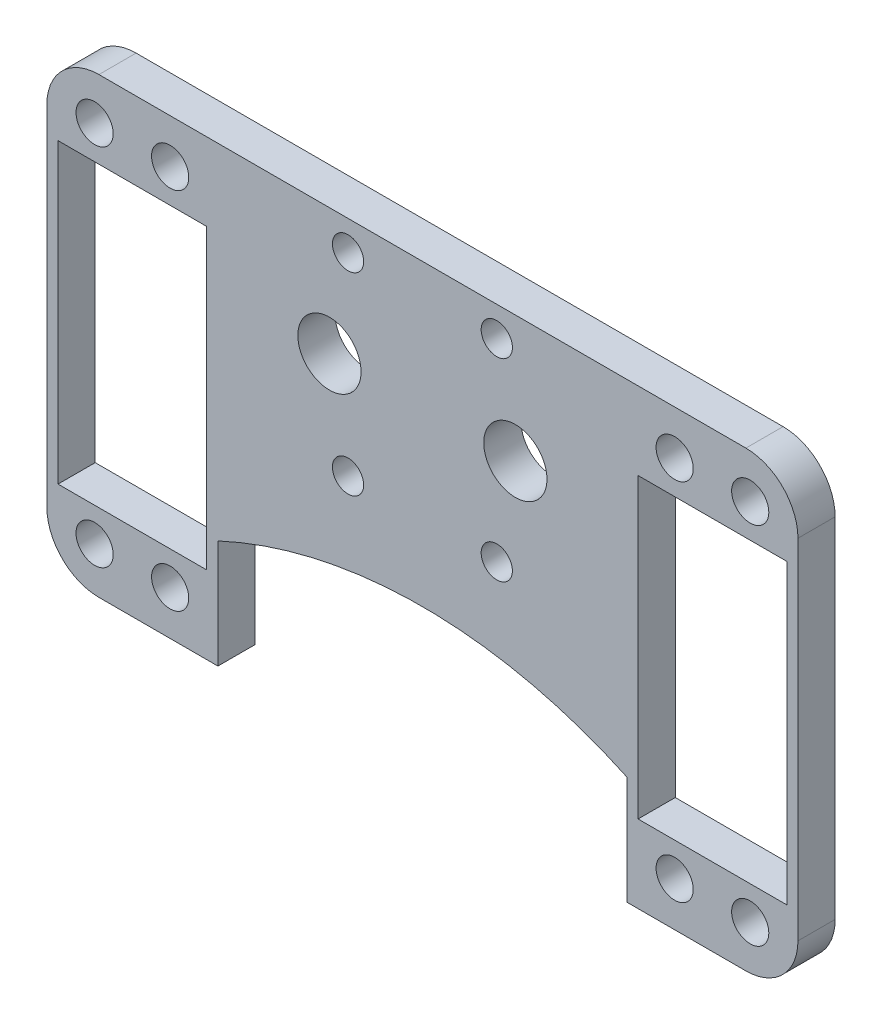
SolidWorks part; units mm, degrees
ref_plane "Front Plane" through (0, 0, 0) normal (0, 0, 1) x (1, 0, 0)
ref_plane "Top Plane" through (0, 0, 0) normal (0, 1, 0) x (1, 0, 0)
ref_plane "Right Plane" through (0, 0, 0) normal (1, 0, 0) x (0, 0, -1)
sketch "Sketch1" plane through (0, 0, 0) normal (0, 0, 1) x (1, 0, 0)
  line L14 (27.058, 13.3488) -> (18.058, 13.3488)
  line L15 (18.058, 13.3488) -> (18.058, 18.3488)
  line L16 (18.058, 18.3488) -> (-18.942, 18.3488)
  line L17 (-18.942, 18.3488) -> (-18.942, 13.3488)
  line L18 (-18.942, 13.3488) -> (-27.942, 13.3488)
  line L19 (-27.942, 13.3488) -> (-27.942, 1.3488)
  line L20 (27.058, 1.3488) -> (27.058, 13.3488)
  line L26 (27.058, -10.6512) -> (27.058, 1.3488)
  line L27 (-27.942, 1.3488) -> (-27.942, -10.6512)
  line L28 (-0.442, -25.6512) -> (-0.442, -85.6512) construction
  line L29 (-27.942, -10.6512) -> (-63.2973, -46.0066)
  line L34 (-63.2973, -46.0066) -> (-51.2973, -58.0066)
  line L35 (62.4134, -46.0066) -> (50.4134, -58.0066)
  line L37 (27.058, -10.6512) -> (62.4134, -46.0066)
  line L38 (-51.2973, -58.0066) -> (50.4134, -58.0066)
  arc A5 (-8.692, 1.3488) -> (-17.192, 1.3488) centre (-12.942, 1.3488) ccw
  arc A6 (16.308, 1.3488) -> (7.808, 1.3488) centre (12.058, 1.3488) ccw
  arc A7 (7.808, 1.3488) -> (16.308, 1.3488) centre (12.058, 1.3488) ccw
  arc A8 (-17.192, 1.3488) -> (-8.692, 1.3488) centre (-12.942, 1.3488) ccw
  circle A9 centre (9.558, -11.6512) radius 2.1
  circle A10 centre (-10.442, -11.6512) radius 2.1
  circle A11 centre (-10.442, 14.3488) radius 2.1
  circle A12 centre (9.558, 14.3488) radius 2.1
  dimension "D1" = 60
  dimension "D4" = 50
extrude "Boss-Extrude1" add sketch "Sketch1" along normal blind 5
sketch "Sketch2" plane through (0, 0, 0) normal (0, 0, -1) x (-1, 0, 0)
  line L0 (-27.058, -22.4869) -> (-27.058, -151.2309)
  line L2 (0.442, -156.8589) -> (0.442, -140.8235) construction
  line L3 (27.942, -22.4869) -> (27.942, -151.2309)
  arc A0 (-27.058, -151.2309) -> (27.942, -151.2309) centre (0.442, -86.8589) ccw
  arc A1 (27.942, -22.4869) -> (-27.058, -22.4869) centre (0.442, -86.8589) ccw
  dimension "D1" = 140
extrude "Cut-Extrude1" cut sketch "Sketch2" against normal blind 5
sketch "Sketch3" plane through (0, 0, 0) normal (0, 0, -1) x (-1, 0, 0)
  line L0 (0.442, -21.8589) -> (0.442, -31.1554) construction
  line L1 (-27.058, -27.5381) -> (-65.3095, -27.5381)
  line L2 (-27.058, -27.5381) -> (-27.058, -60.3042)
  line L3 (-27.058, -60.3042) -> (-65.3095, -60.3042)
  line L4 (-65.3095, -27.5381) -> (-65.3095, -60.3042)
  line L5 (-27.058, -27.5381) -> (-65.3095, -60.3042) construction
  line L6 (-27.058, -60.3042) -> (-65.3095, -27.5381) construction
  line L7 (27.942, -60.3042) -> (66.1934, -27.5381) construction
  line L8 (27.942, -27.5381) -> (66.1934, -60.3042) construction
  line L9 (66.1934, -27.5381) -> (66.1934, -60.3042)
  line L10 (27.942, -60.3042) -> (66.1934, -60.3042)
  line L11 (27.942, -27.5381) -> (27.942, -60.3042)
  line L12 (27.942, -27.5381) -> (66.1934, -27.5381)
  point P4 (-46.1838, -43.9212)
  point P16 (47.0677, -43.9212)
extrude "Cut-Extrude2" cut sketch "Sketch3" against normal blind 10
sketch "Sketch4" plane through (0, 0, 0) normal (0, 0, -1) x (-1, 0, 0)
  line L0 (0.442, -21.8589) -> (0.442, -38.1252) construction
  line L1 (27.942, -27.5381) -> (50.942, -27.5381)
  line L2 (50.942, -27.5381) -> (50.942, 27.4619)
  line L3 (-50.058, -27.5381) -> (-50.058, 27.4619)
  line L4 (-27.058, -27.5381) -> (-50.058, -27.5381)
  line L5 (45.942, 32.4619) -> (-45.058, 32.4619)
  line L12 (-27.058, 13.3488) -> (-27.058, -10.6512)
  line L13 (27.942, -10.6512) -> (27.942, 13.3488)
  line L14 (27.942, 13.3488) -> (18.942, 13.3488)
  line L15 (18.942, 13.3488) -> (18.942, 18.3488)
  line L16 (18.942, 18.3488) -> (-18.058, 18.3488)
  line L17 (-18.058, 18.3488) -> (-18.058, 13.3488)
  line L18 (-18.058, 13.3488) -> (-27.058, 13.3488)
  line L19 (-27.058, 13.3488) -> (-27.058, -10.6512)
  line L20 (27.942, -10.6512) -> (27.942, 13.3488)
  line L21 (27.942, 13.3488) -> (18.942, 13.3488)
  line L22 (18.942, 13.3488) -> (18.942, 18.3488)
  line L23 (18.942, 18.3488) -> (-18.058, 18.3488)
  line L24 (-18.058, 18.3488) -> (-18.058, 13.3488)
  line L25 (-18.058, 13.3488) -> (-27.058, 13.3488)
  line L33 (-27.058, -10.6512) -> (-43.9449, -27.5381)
  line L34 (-27.058, -10.6512) -> (-43.9449, -27.5381)
  line L35 (-43.9449, -27.5381) -> (-27.058, -27.5381)
  line L36 (-43.9449, -27.5381) -> (-27.058, -27.5381)
  line L37 (-27.058, -27.5381) -> (-27.058, -22.4869)
  line L38 (-27.058, -27.5381) -> (-27.058, -22.4869)
  line L39 (27.942, -22.4869) -> (27.942, -27.5381)
  line L40 (27.942, -22.4869) -> (27.942, -27.5381)
  line L41 (27.942, -27.5381) -> (44.8289, -27.5381)
  line L42 (27.942, -27.5381) -> (44.8289, -27.5381)
  line L43 (44.8289, -27.5381) -> (27.942, -10.6512)
  line L44 (44.8289, -27.5381) -> (27.942, -10.6512)
  arc A1 (50.942, 27.4619) -> (45.942, 32.4619) centre (45.942, 27.4619) ccw
  arc A4 (-50.058, 27.4619) -> (-45.058, 32.4619) centre (-45.058, 27.4619) cw
  arc A5 (27.942, -22.4869) -> (-27.058, -22.4869) centre (0.442, -86.8589) ccw
  arc A6 (27.942, -22.4869) -> (-27.058, -22.4869) centre (0.442, -86.8589) ccw
  point P20 (50.942, 32.4619)
  point P26 (-50.058, 32.4619)
  line M12 (-27.058, 13.3488) -> (-27.058, -10.6512)
  line M14 (27.942, -10.6512) -> (27.942, 13.3488)
  line M15 (27.942, 13.3488) -> (18.942, 13.3488)
  line M16 (18.942, 13.3488) -> (18.942, 18.3488)
  line M17 (18.942, 18.3488) -> (-18.058, 18.3488)
  line M18 (-18.058, 18.3488) -> (-18.058, 13.3488)
  line M19 (-18.058, 13.3488) -> (-27.058, 13.3488)
  dimension "D4" = 5
  dimension "D1" = 23
  dimension "D2" = 60
  dimension "D3" = 0
extrude "Boss-Extrude2" add sketch "Sketch4" against normal blind 5 contours A4 L3 L4 L1 L2 A1 L5 M12 M19 M18 M17 M16 M15 M14
sketch "Sketch5" plane through (0, 0, 5) normal (0, 0, 1) x (1, 0, 0)
  line L0 (-50.942, -27.5381) -> (-50.942, 27.4619) construction
  line L1 (-50.942, 18.3488) -> (50.9149, 18.3488)
  line L2 (-50.942, 18.3488) -> (-50.942, 33.5751)
  line L3 (-50.942, 33.5751) -> (50.9149, 33.5751)
  line L4 (50.9149, 18.3488) -> (50.9149, 33.5751)
  line L5 (-50.942, 18.3488) -> (50.9149, 33.5751) construction
  line L6 (-50.942, 33.5751) -> (50.9149, 18.3488) construction
  point P4 (-0.0135, 25.9619)
extrude "Cut-Extrude3" cut sketch "Sketch5" against normal blind 10
sketch "Sketch6" plane through (0, 0, 5) normal (0, 0, 1) x (1, 0, 0)
  line L0 (50.058, -27.5381) -> (27.058, -27.5381) construction
  line L1 (27.058, -22.4869) -> (27.058, -27.5381) construction
  line L2 (-27.942, -27.5381) -> (-50.942, -27.5381) construction
  line L3 (-27.942, -27.5381) -> (-27.942, -22.4869) construction
  line L4 (50.058, -27.5381) -> (27.058, -27.5381)
  line L5 (27.058, -22.4869) -> (27.058, -27.5381)
  line L6 (-27.942, -27.5381) -> (-50.942, -27.5381)
  line L7 (-27.942, -27.5381) -> (-27.942, -22.4869)
  line L8 (50.058, -42.5381) -> (12.058, -42.5381)
  line L11 (-12.942, -42.5381) -> (-50.942, -42.5381)
  line L12 (-50.942, -42.5381) -> (-50.942, -27.5381)
  line L13 (50.058, -42.5381) -> (50.058, -27.5381)
  line L14 (-12.942, -42.5381) -> (12.058, -42.5381)
  line L15 (-12.942, -42.5381) -> (-12.942, -33.2982) construction
  line L16 (12.058, -33.2982) -> (12.058, -42.5381) construction
  arc A0 (27.058, -22.4869) -> (-27.942, -22.4869) centre (-0.442, -86.8589) ccw construction
  arc A1 (27.058, -22.4869) -> (-27.942, -22.4869) centre (-0.442, -86.8589) ccw
  arc A3 (12.058, -33.2982) -> (-12.942, -33.2982) centre (-0.442, -86.8589) ccw construction
  dimension "D1" = 15
extrude "Boss-Extrude3" add sketch "Sketch6" against normal blind 5
sketch "Sketch7" plane through (0, 0, 5) normal (0, 0, 1) x (1, 0, 0)
  line L5 (-0.442, -42.5381) -> (-0.442, -34.3922) construction
  line L12 (-50.942, -42.5381) -> (50.058, -42.5381) construction
  line L20 (-27.942, -27.9628) -> (-27.942, -42.5381)
  line L21 (27.058, -27.9628) -> (27.058, -42.5381)
  line L22 (-27.942, -42.5381) -> (27.058, -42.5381)
  arc A0 (27.058, -27.9628) -> (-27.942, -27.9628) centre (-0.442, -86.8589) ccw
extrude "Cut-Extrude4" cut sketch "Sketch7" against normal blind 5
sketch "Sketch8" plane through (0, 0, 0) normal (0, 0, -1) x (-1, 0, 0)
  line L0 (29.442, -12.0947) -> (49.442, -12.0947) construction
  line L1 (29.442, -30.5947) -> (29.442, 6.4053) construction
  line L2 (49.442, 6.4053) -> (49.442, -30.5947) construction
  line L3 (30.442, 7.9053) -> (48.442, 7.9053) construction
  line L4 (49.442, -32.0947) -> (29.442, -32.0947)
  line L5 (49.442, -32.0947) -> (49.442, 7.9053)
  line L6 (49.442, 7.9053) -> (29.442, 7.9053)
  line L7 (29.442, -32.0947) -> (29.442, 7.9053)
  line L8 (49.442, -32.0947) -> (29.442, 7.9053) construction
  line L9 (49.442, 7.9053) -> (29.442, -32.0947) construction
  line L10 (0.442, 18.3311) -> (0.442, 31.4799) construction
  line L11 (-27.058, 18.3488) -> (27.942, 18.3134) construction
  line L12 (-48.558, 7.9053) -> (-28.558, -32.0947) construction
  line L13 (-48.558, -32.0947) -> (-28.558, 7.9053) construction
  line L14 (-28.558, -12.0947) -> (-48.558, -12.0947) construction
  line L15 (-28.558, -32.0947) -> (-28.558, 7.9053)
  line L16 (-48.558, 7.9053) -> (-28.558, 7.9053)
  line L17 (-48.558, -32.0947) -> (-48.558, 7.9053)
  line L18 (-48.558, -32.0947) -> (-28.558, -32.0947)
  circle A0 centre (44.522, 12.4053) radius 2.5
  circle A1 centre (34.362, 12.4053) radius 2.5
  circle A2 centre (34.362, -36.5947) radius 2.5
  circle A3 centre (44.522, -36.5947) radius 2.5
  circle A4 centre (-43.638, -36.5947) radius 2.5
  circle A5 centre (-33.478, -36.5947) radius 2.5
  circle A6 centre (-33.478, 12.4053) radius 2.5
  circle A7 centre (-43.638, 12.4053) radius 2.5
  point P6 (39.442, -12.0947)
  point P43 (-38.558, -12.0947)
  dimension "D1" = 0
  dimension "D2" = 0
extrude "Cut-Extrude5" cut sketch "Sketch8" against normal blind 5
fillet "Fillet2" radius 7 4 edges at (-50.942, -42.5381, 2.5) (-50.942, 18.3488, 2.5) (50.058, -42.5381, 2.5) (50.058, 18.3488, 2.5)
